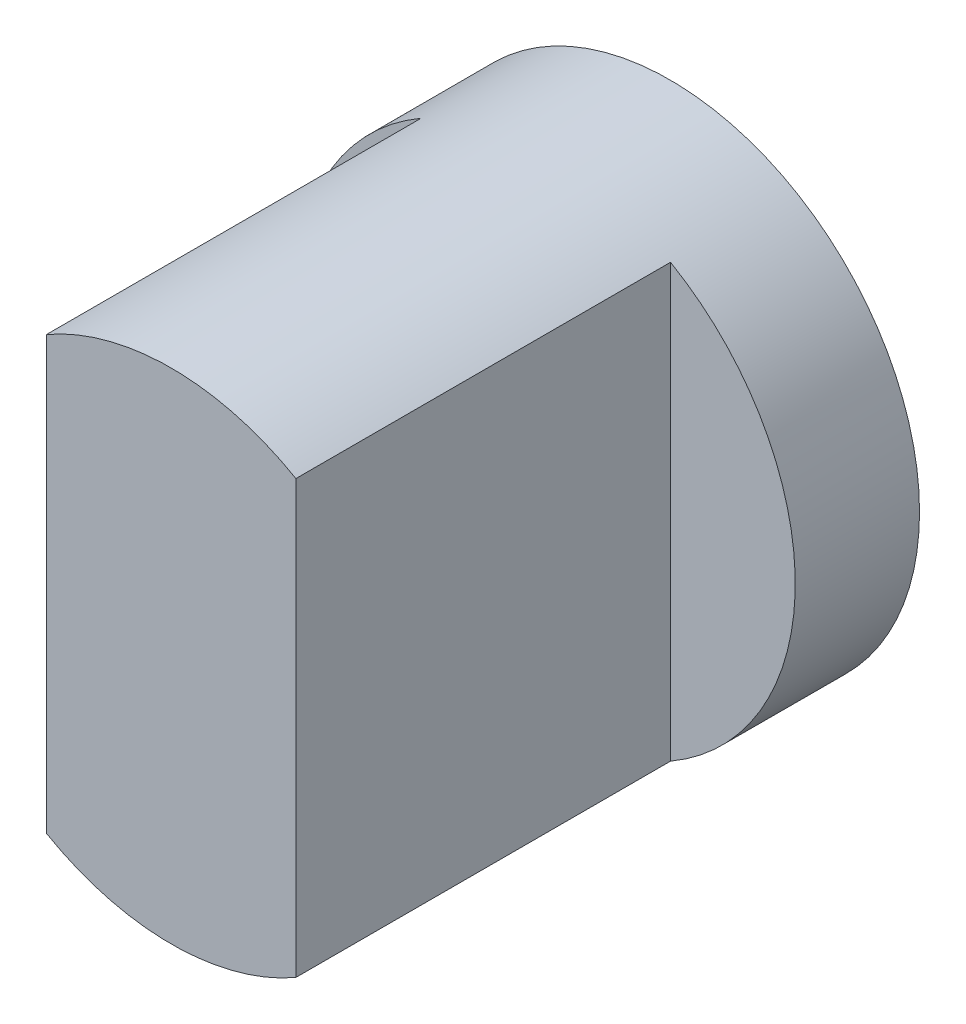
SolidWorks part; units mm, degrees
ref_plane "Front" through (0, 0, 0) normal (0, 0, 1) x (1, 0, 0)
ref_plane "Top" through (0, 0, 0) normal (0, 1, 0) x (1, 0, 0)
ref_plane "Right" through (0, 0, 0) normal (1, 0, 0) x (0, 0, -1)
sketch "Sketch1" plane through (0, 0, 0) normal (0, 0, 1) x (1, 0, 0)
  circle A0 centre (0, 0) radius 2
  dimension "D1" = 4
extrude "Boss-Extrude1" add sketch "Sketch1" along normal blind 4
sketch "Sketch2" plane through (0, 0, 0) normal (0, 1, 0) x (1, 0, 0)
  line L0 (-2, -4) -> (2, -4) construction
  line L1 (-1, -5) -> (1, -5)
  line L5 (-1, -5) -> (1, -3) construction
  line L6 (-1, -3) -> (1, -5) construction
  line L7 (-1, -3) -> (-1, -0.9964)
  line L8 (-1, -0.9964) -> (-2, -0.9964)
  line L9 (-2, 0) -> (-2, -4) construction
  line L10 (-2, -0.9964) -> (-2, -5)
  line L11 (-2, -5) -> (-1, -5)
  line L12 (1, -3) -> (1, -0.9964)
  line L13 (1, -0.9964) -> (2, -0.9964)
  line L14 (2, -4) -> (2, 0) construction
  line L15 (2, -0.9964) -> (2, -5)
  line L16 (2, -5) -> (1, -5)
  line L17 (1, -3) -> (1, -4)
  line L18 (1, -4) -> (-1, -4)
  line L19 (-1, -4) -> (-1, -3)
  point P0 (0, -4)
  dimension "D1" = 2
  dimension "D2" = 2
extrude "Cut-Extrude2" cut sketch "Sketch2" against normal mid plane 4
